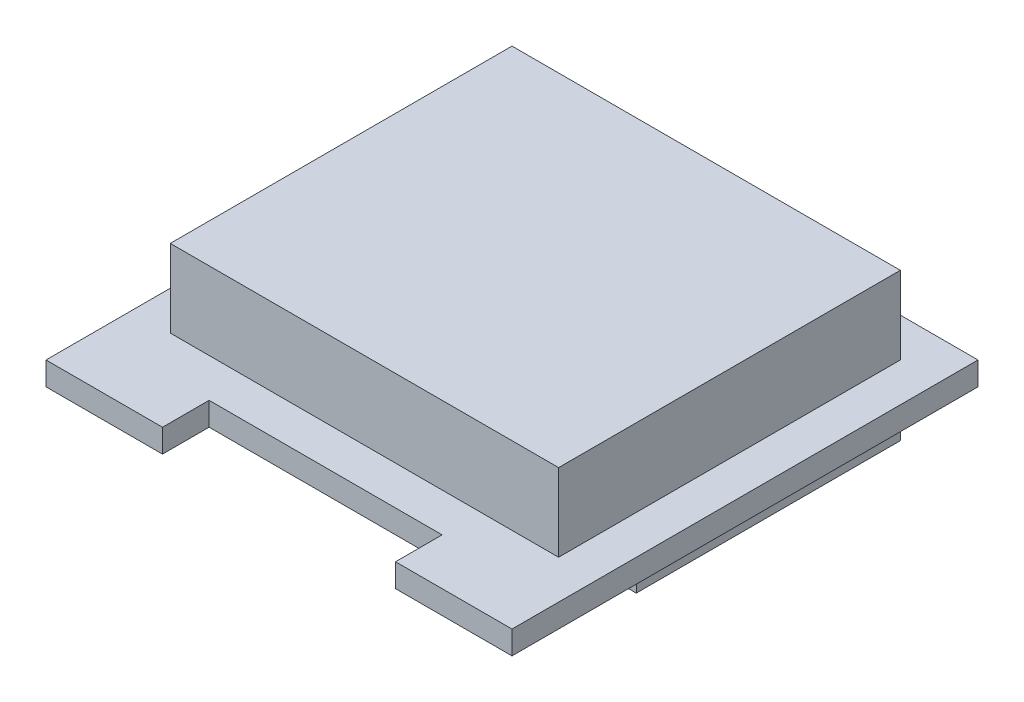
SolidWorks part; units mm, degrees
ref_plane "Front Plane" through (0, 0, 0) normal (0, 0, 1) x (1, 0, 0)
ref_plane "Top Plane" through (0, 0, 0) normal (0, 1, 0) x (1, 0, 0)
ref_plane "Right Plane" through (0, 0, 0) normal (1, 0, 0) x (0, 0, -1)
sketch "Sketch1" plane through (0, 0, 0) normal (0, 1, 0) x (1, 0, 0)
  line L1 (0, 0) -> (30, 0)
  line L2 (0, 0) -> (0, 30)
  line L3 (0, 30) -> (30, 30)
  line L4 (30, 0) -> (30, 30)
  line L5 (7.5, 0) -> (22.5, 0)
  line L6 (7.5, 0) -> (7.5, 3)
  line L7 (7.5, 3) -> (22.5, 3)
  line L8 (22.5, 0) -> (22.5, 3)
  point P9 (15, 3)
  point P10 (15, 30)
  dimension "D1" = 30
  dimension "D2" = 30
  dimension "D3" = 15
  dimension "D4" = 3
extrude "Boss-Extrude1" add sketch "Sketch1" along normal blind 1.5 contours L8 L1 L4 L3 L2 L6 L7
sketch "Sketch2" plane through (0, 1.5, 0) normal (0, 1, 0) x (1, 0, 0)
  line L16 (27.5, 2.5) -> (27.5, 27.5)
  line L17 (27.5, 27.5) -> (2.5, 27.5)
  line L18 (2.5, 27.5) -> (2.5, 2.5)
  line L19 (5, 5.5) -> (25, 5.5)
  line L20 (27.5, 2.5) -> (27.5, 27.5)
  line L21 (27.5, 27.5) -> (2.5, 27.5)
  line L22 (2.5, 27.5) -> (2.5, 2.5)
  line L23 (2.5, 5.5) -> (27.5, 5.5)
  line L24 (25, 5.5) -> (25, 2.5)
  line L25 (25, 5.5) -> (25, 2.5)
  line L26 (25, 2.5) -> (27.5, 2.5)
  line L27 (25, 2.5) -> (27.5, 2.5)
  line L28 (2.5, 2.5) -> (5, 2.5)
  line L29 (2.5, 2.5) -> (5, 2.5)
  line L30 (5, 2.5) -> (5, 5.5)
  line L31 (5, 2.5) -> (5, 5.5)
  dimension "D1" = 2.5
extrude "Boss-Extrude2" add sketch "Sketch2" along normal blind 5 contours L22 L23 L20 L21
sketch "Sketch3" plane through (0, 0, 0) normal (0, -1, 0) x (1, 0, 0)
  line L8 (2.5, -10.5) -> (27.5, -10.5)
  line L11 (27.5, -27.5) -> (27.5, 0)
  line L12 (2.5, -27.5) -> (27.5, -27.5)
  line L13 (2.5, 0) -> (2.5, -27.5)
  line L14 (27.5, -27.5) -> (27.5, 0)
  line L15 (2.5, -27.5) -> (27.5, -27.5)
  line L16 (2.5, 0) -> (2.5, -27.5)
  dimension "D2" = 17
  dimension "D1" = 2.5
extrude "Boss-Extrude3" add sketch "Sketch3" along normal blind 3 contours L8 L16 L15 L14
